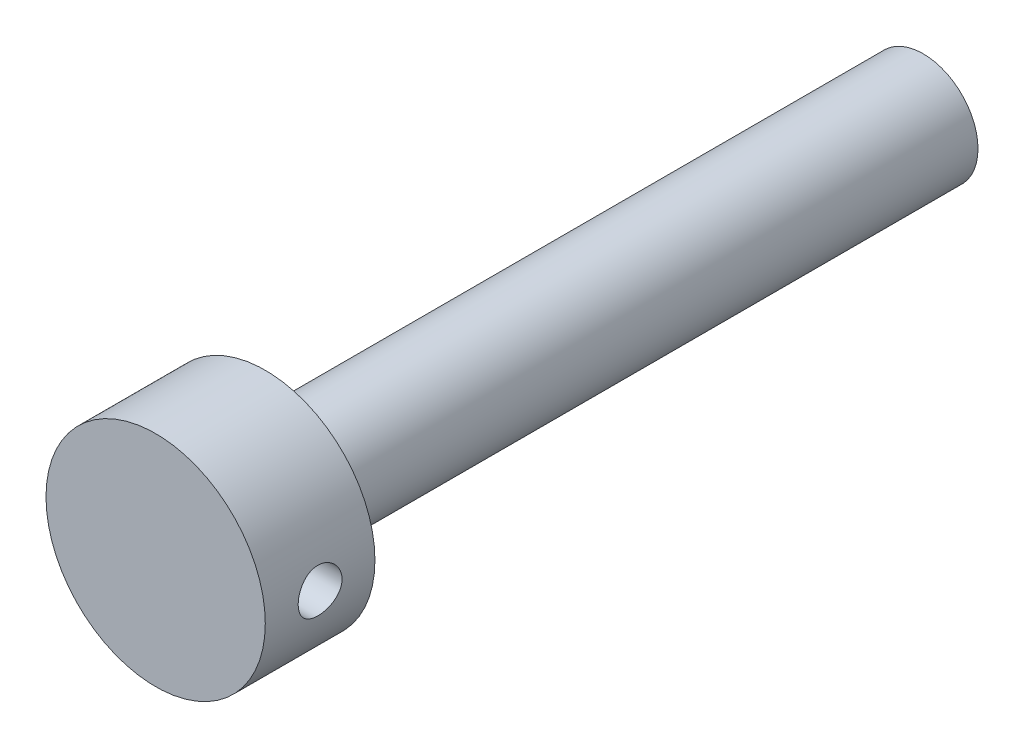
SolidWorks part; units mm, degrees
material "AISI 1020"
ref_plane "Front Plane" through (0, 0, 0) normal (0, 0, 1) x (1, 0, 0)
ref_plane "Top Plane" through (0, 0, 0) normal (0, 1, 0) x (1, 0, 0)
ref_plane "Right Plane" through (0, 0, 0) normal (1, 0, 0) x (0, 0, -1)
sketch "Sketch1" plane through (0, 0, 0) normal (0, 0, 1) x (1, 0, 0)
  circle A0 centre (0, 0) radius 5
  dimension "D1" = 10
extrude "Boss-Extrude1" add sketch "Sketch1" along normal mid plane 60
sketch "Sketch3" plane through (0, 0, 30) normal (0, 0, 1) x (1, 0, 0)
  circle A0 centre (0, 0) radius 10
  dimension "D1" = 20
extrude "Boss-Extrude3" add sketch "Sketch3" along normal blind 10
sketch "Sketch4" plane through (0, 0, 0) normal (1, 0, 0) x (0, 0, -1)
  line L0 (-40, 10) -> (-40, -10) construction
  circle A0 centre (-35, 0) radius 2
  dimension "D1" = 4
  dimension "D2" = 5
extrude "Cut-Extrude1" cut sketch "Sketch4" against normal through all both and the other way through all
